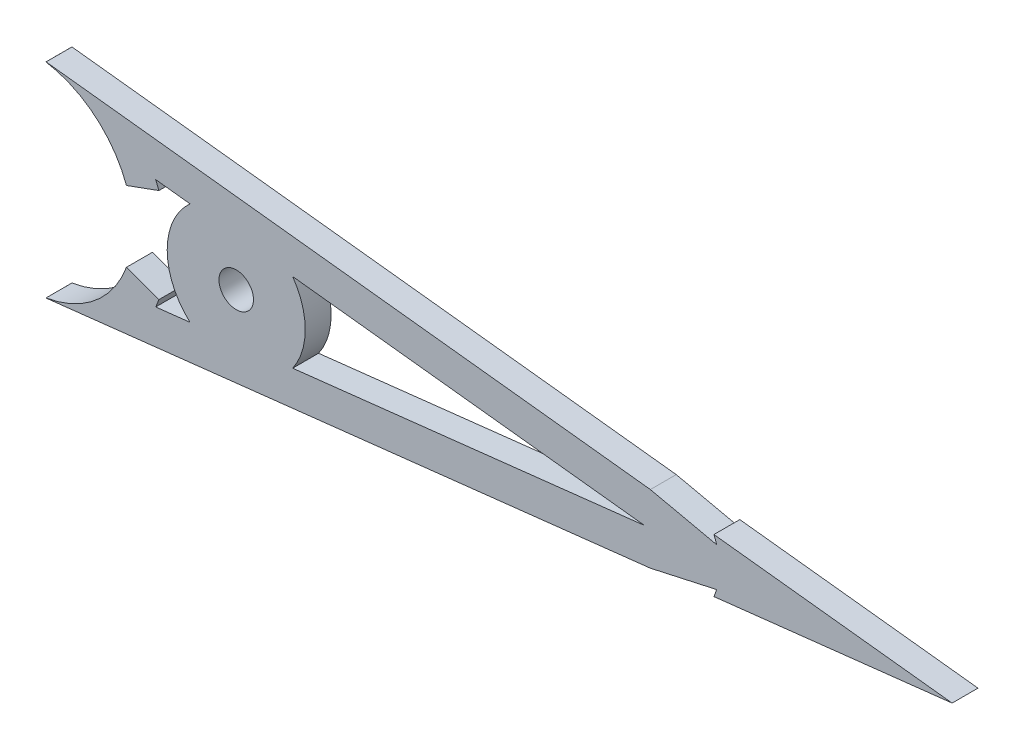
SolidWorks part; units mm, degrees
material "PVC 0.007 Plasticized"
ref_plane "Front Plane" through (0, 0, 0) normal (0, 0, 1) x (1, 0, 0)
ref_plane "Top Plane" through (0, 0, 0) normal (0, 1, 0) x (1, 0, 0)
ref_plane "Right Plane" through (0, 0, 0) normal (1, 0, 0) x (0, 0, -1)
sketch "Sketch1" plane through (0, 0, 0) normal (0, 0, 1) x (1, 0, 0)
  line L0 (0, 0) -> (-38.1, 0) construction
  line L1 (0, 0) -> (76.2, 0) construction
  line L2 (76.2, 0) -> (131.7244, 0) construction
  line L3 (131.7244, 0) -> (87.8966, 4.9476)
  line L4 (131.7244, 0) -> (87.8966, -4.9476)
  line L5 (75.1163, 0) -> (10.3873, 7.3071)
  line L6 (75.1163, 0) -> (10.3873, -7.3071)
  line L7 (76.2, 6.268) -> (88.385, 3.5799)
  line L8 (76.2, -6.268) -> (88.385, -3.5799)
  line L9 (-20.1989, 6.5155) -> (-14.2318, 8.6873)
  line L10 (-20.1989, -6.5155) -> (-14.2318, -8.6873)
  line L11 (-8.4969, 9.4389) -> (-14.8172, 10.1523)
  line L12 (75.1163, 0) -> (-14.8172, 10.1523) construction
  line L13 (-8.4969, -9.4389) -> (-14.8172, -10.1523)
  line L14 (75.1163, 0) -> (-14.8172, -10.1523) construction
  line L15 (76.2, -6.268) -> (-35.9631, -18.9298)
  line L16 (131.7244, 0) -> (-35.9631, -18.9298) construction
  line L17 (76.2, 6.268) -> (-35.9631, 18.9298)
  line L18 (131.7244, 0) -> (-35.9631, 18.9298) construction
  line L19 (-38.1, 0) -> (-14.2318, 8.6873) construction
  circle A0 centre (0, 0) radius 3.175
  arc A1 (-8.4969, 9.4389) -> (-8.4969, -9.4389) centre (0, 0) ccw
  arc A2 (-35.9631, -18.9298) -> (-20.1989, -6.5155) centre (-38.1, 0) ccw
  arc A4 (-14.8172, -10.1523) -> (-14.2318, -8.6873) centre (-38.1, 0) ccw
  arc A5 (87.8966, -4.9476) -> (88.385, -3.5799) centre (76.2, 0) ccw
  arc A6 (-14.2318, 8.6873) -> (-14.8172, 10.1523) centre (-38.1, 0) ccw
  arc A7 (-14.8172, -10.1523) -> (-14.8172, 10.1523) centre (-38.1, 0) ccw construction
  arc A8 (-20.1989, 6.5155) -> (-35.9631, 18.9298) centre (-38.1, 0) ccw
  arc A9 (-35.9631, -18.9298) -> (-35.9631, 18.9298) centre (-38.1, 0) ccw construction
  arc A10 (10.3873, -7.3071) -> (10.3873, 7.3071) centre (0, 0) ccw
  arc A11 (88.385, 3.5799) -> (87.8966, 4.9476) centre (76.2, 0) ccw
  dimension "D3" = 38.1
  dimension "D4" = 6.35
  dimension "D5" = 25.4
  dimension "D6" = 76.2
  dimension "D8" = 25.4
  dimension "D1" = 38.1
  dimension "D2" = 6.35
  dimension "D7" = 131.7244
  dimension "D9" = 6
  dimension "D10" = 20
extrude "Boss-Extrude2" add sketch "Sketch1" against normal blind 4.7625
fillet "Fillet1" radius 0.0127 2 edges at (-35.9631, 18.9298, -2.3813) (-35.9631, -18.9298, -2.3813)
